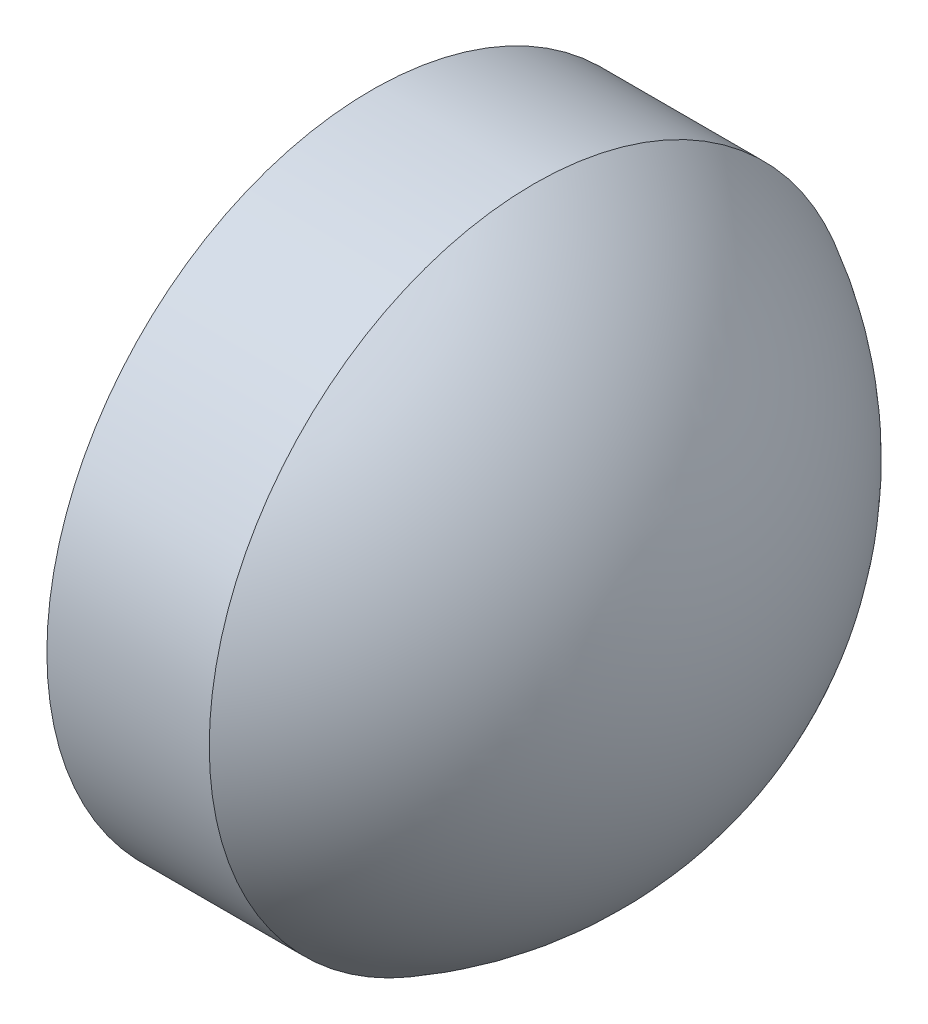
SolidWorks part; units mm, degrees
ref_plane "前视基准面" through (0, 0, 0) normal (0, 0, 1) x (1, 0, 0)
ref_plane "上视基准面" through (0, 0, 0) normal (0, 1, 0) x (1, 0, 0)
ref_plane "右视基准面" through (0, 0, 0) normal (1, 0, 0) x (0, 0, -1)
sketch "草图1" plane through (0, 0, 0) normal (0, 0, 1) x (1, 0, 0)
  line L0 (359.8644, 32.4014) -> (362.5619, 32.4014) construction
  line L1 (360.2925, 32.4014) -> (360.2925, 34.4014)
  line L2 (360.2925, 34.4014) -> (361.2925, 34.4014)
  line L3 (362.4925, 32.4014) -> (360.2925, 32.4014)
  arc A0 (362.4925, 32.4014) -> (361.2925, 34.4014) centre (360.2259, 32.4014) ccw
revolve "旋转1" add sketch "草图1" angle 360 about L0
